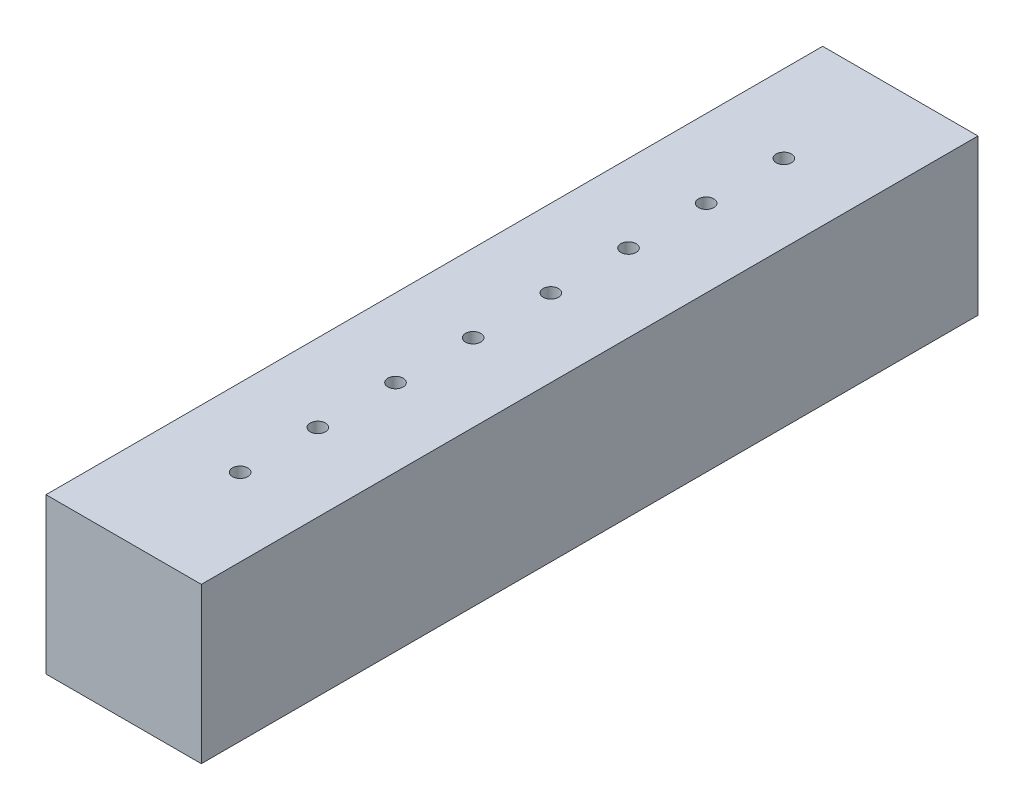
SolidWorks part; units mm, degrees
ref_plane "Front Plane" through (0, 0, 0) normal (0, 0, 1) x (1, 0, 0)
ref_plane "Top Plane" through (0, 0, 0) normal (0, 1, 0) x (1, 0, 0)
ref_plane "Right Plane" through (0, 0, 0) normal (1, 0, 0) x (0, 0, -1)
sketch "Sketch1" plane through (0, 0, 0) normal (0, 1, 0) x (1, 0, 0)
  line L1 (25.4, -127) -> (-25.4, -127)
  line L2 (25.4, -127) -> (25.4, 127)
  line L3 (25.4, 127) -> (-25.4, 127)
  line L4 (-25.4, -127) -> (-25.4, 127)
  line L5 (25.4, -127) -> (-25.4, 127) construction
  line L6 (25.4, 127) -> (-25.4, -127) construction
  point P0 (0, 0)
  dimension "D1" = 254
  dimension "D2" = 50.8
extrude "Boss-Extrude1" add sketch "Sketch1" along normal blind 50.8
sketch "Sketch3" plane through (0, 50.8, 0) normal (0, 1, 0) x (1, 0, 0)
  line L0 (0, 132.1106) -> (0, -135.4133) construction
  line L1 (25.4, 127) -> (-25.4, 127) construction
  circle A0 centre (0, 88.9) radius 2.5019
  circle A1 centre (0, 63.5) radius 2.5019
  circle A2 centre (0, 38.1) radius 2.5019
  circle A3 centre (0, 12.7) radius 2.5019
  circle A4 centre (0, -12.7) radius 2.5019
  circle A5 centre (0, -38.1) radius 2.5019
  circle A6 centre (0, -63.5) radius 2.5019
  circle A7 centre (0, -88.9) radius 2.5019
  dimension "D2" = 5.0038
  dimension "D1" = 25.4
  dimension "D3" = 38.1
  dimension "D4" = 25.4
  dimension "D5" = 25.4
  dimension "D6" = 25.4
  dimension "D7" = 25.4
  dimension "D8" = 25.4
  dimension "D9" = 25.4
extrude "Cut-Extrude1" cut sketch "Sketch3" against normal blind 8.89
